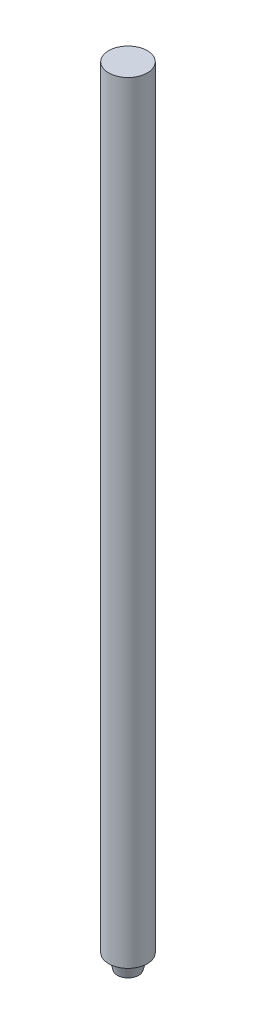
SolidWorks part; units mm, degrees
ref_plane "Plano frontal" through (0, 0, 0) normal (0, 0, 1) x (1, 0, 0)
ref_plane "Plano superior" through (0, 0, 0) normal (0, 1, 0) x (1, 0, 0)
ref_plane "Plano direito" through (0, 0, 0) normal (1, 0, 0) x (0, 0, -1)
sketch "Esboço1" plane through (0, 0, 0) normal (0, 1, 0) x (1, 0, 0)
  circle A0 centre (0, 0) radius 4
  dimension "D1" = 8
extrude "Extrusão1" add sketch "Esboço1" against normal blind 159.86
sketch "Esboço3" plane through (0, -159.86, 0) normal (0, -1, 0) x (1, 0, 0)
  circle A0 centre (0, 0) radius 3
  dimension "D1" = 6
extrude "Extrusão2" add sketch "Esboço3" along normal blind 3 draft 15
